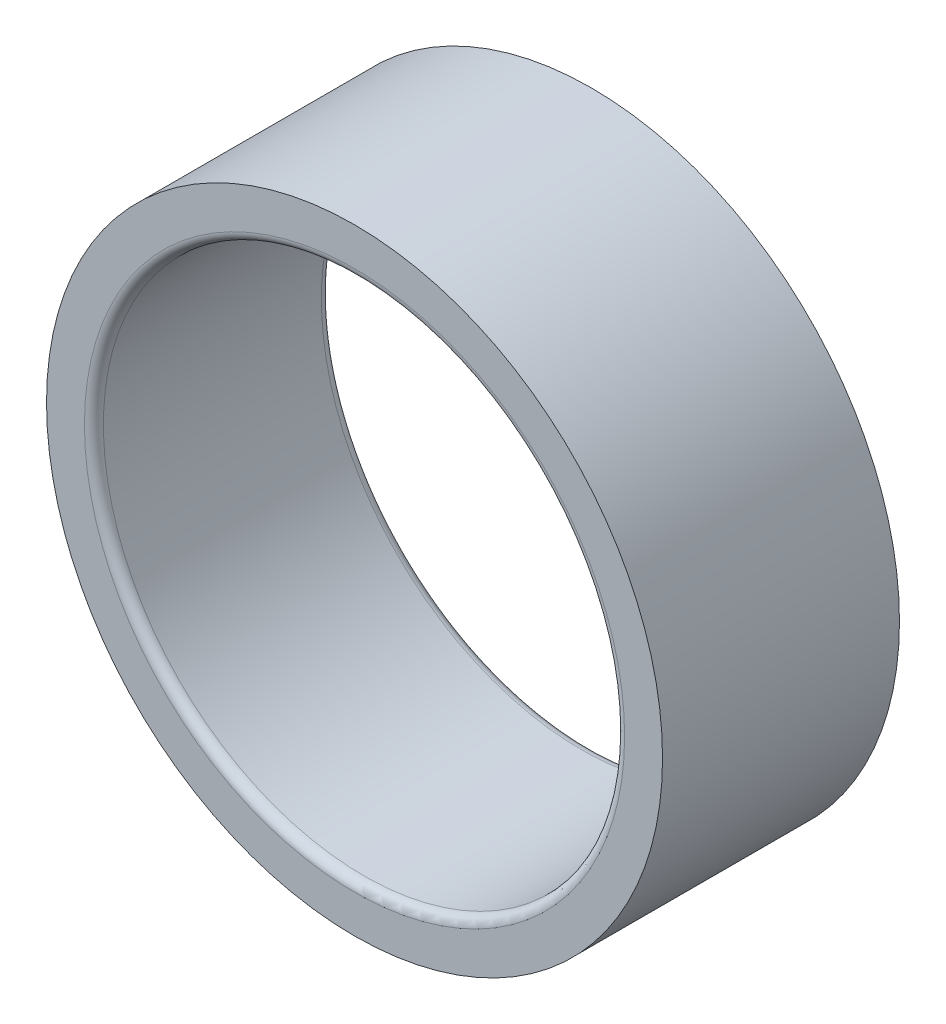
SolidWorks part; units mm, degrees
ref_plane "Front Plane" through (0, 0, 0) normal (0, 0, 1) x (1, 0, 0)
ref_plane "Top Plane" through (0, 0, 0) normal (0, 1, 0) x (1, 0, 0)
ref_plane "Right Plane" through (0, 0, 0) normal (1, 0, 0) x (0, 0, -1)
sketch "Sketch1" plane through (0, 0, 0) normal (0, 0, 1) x (1, 0, 0)
  circle A0 centre (0, 0) radius 65
  dimension "D1" = 130
extrude "Extrude1" add sketch "Sketch1" along normal blind 50
sketch "Sketch2" plane through (0, 0, 50) normal (0, 0, 1) x (1, 0, 0)
  circle A0 centre (0, 0) radius 55
  dimension "D1" = 110
extrude "Extrude2" cut sketch "Sketch2" against normal through all
fillet "Fillet1" radius 2 2 edges at (55, 0, 0) (55, 0, 50)
